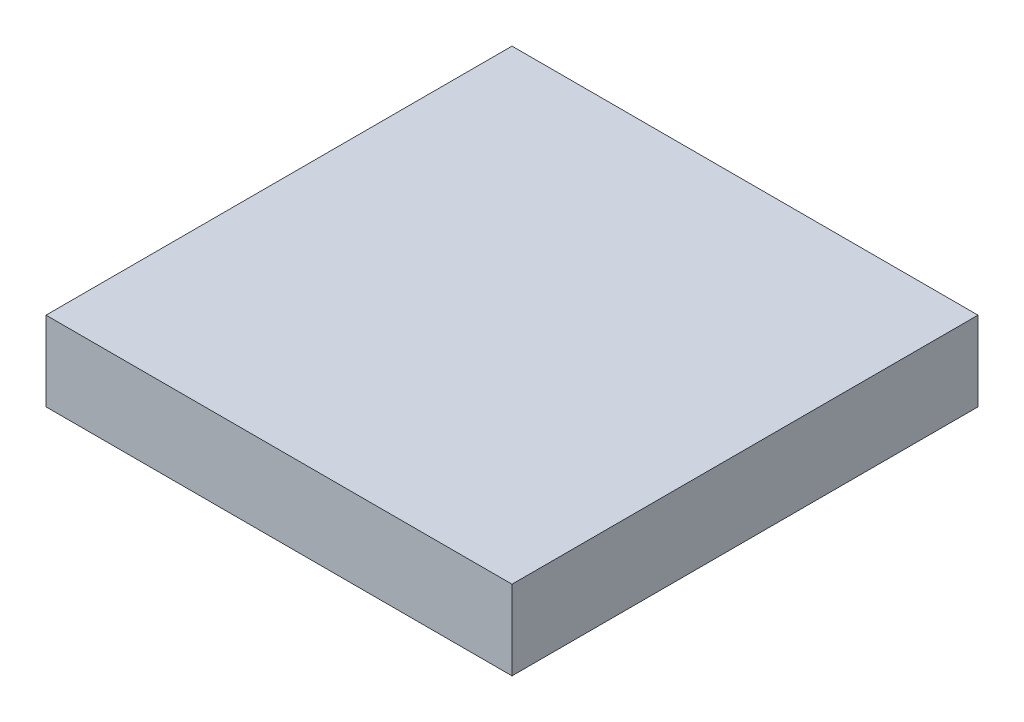
SolidWorks part; units mm, degrees
ref_plane "Front Plane" through (0, 0, 0) normal (0, 0, 1) x (1, 0, 0)
ref_plane "Top Plane" through (0, 0, 0) normal (0, 1, 0) x (1, 0, 0)
ref_plane "Right Plane" through (0, 0, 0) normal (1, 0, 0) x (0, 0, -1)
sketch "Sketch1" plane through (0, 0, 0) normal (0, 1, 0) x (1, 0, 0)
  line L1 (11, -11) -> (-11, -11)
  line L2 (11, -11) -> (11, 11)
  line L3 (11, 11) -> (-11, 11)
  line L4 (-11, -11) -> (-11, 11)
  line L5 (11, -11) -> (-11, 11) construction
  line L6 (11, 11) -> (-11, -11) construction
  point P0 (0, 0)
  dimension "D1" = 22
extrude "Boss-Extrude1" add sketch "Sketch1" along normal blind 3.75
